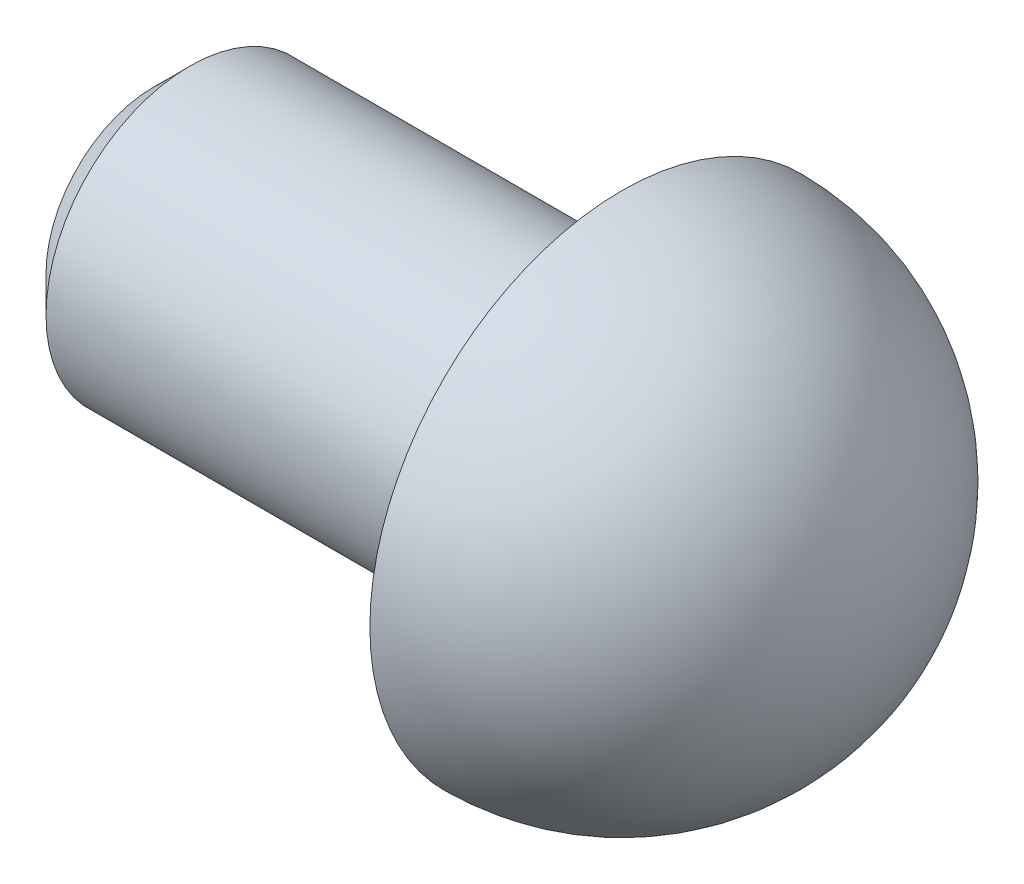
SolidWorks part; units mm, degrees
ref_plane "Front Plane" through (0, 0, 0) normal (0, 0, 1) x (1, 0, 0)
ref_plane "Top Plane" through (0, 0, 0) normal (0, 1, 0) x (1, 0, 0)
ref_plane "Right Plane" through (0, 0, 0) normal (1, 0, 0) x (0, 0, -1)
sketch "Sketch1" plane through (0, 0, 0) normal (0, 0, 1) x (1, 0, 0)
  line L0 (-6.5, 0) -> (-6.5, 2)
  line L1 (-6.5, 2) -> (0, 2)
  line L2 (0, 2) -> (0, 3.5)
  line L3 (-6.5, 0) -> (3.5, 0)
  arc A0 (3.5, 0) -> (0, 3.5) centre (0, 0) ccw
  dimension "D1" = 7
  dimension "D2" = 6.5
  dimension "D3" = 2
revolve "Revolve1" add sketch "Sketch1" angle 360 about L3
chamfer "Chamfer1" distance 0.5 angle 45 1 edges at (-6.5, 0, 2)
